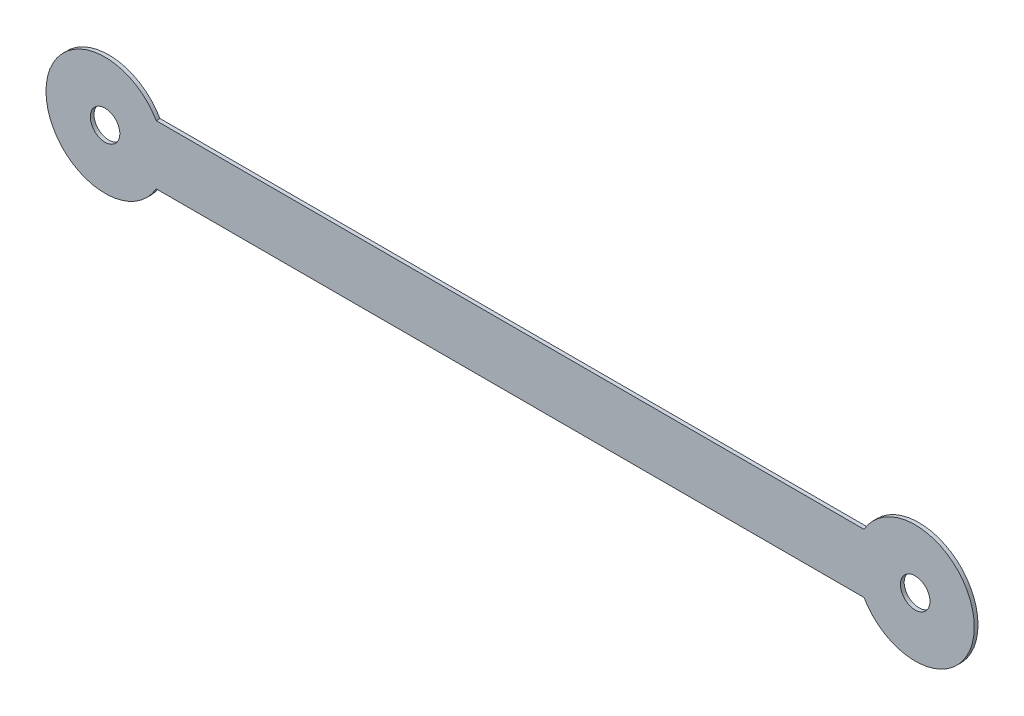
SolidWorks part; units mm, degrees
ref_plane "Front Plane" through (0, 0, 0) normal (0, 0, 1) x (1, 0, 0)
ref_plane "Top Plane" through (0, 0, 0) normal (0, 1, 0) x (1, 0, 0)
ref_plane "Right Plane" through (0, 0, 0) normal (1, 0, 0) x (0, 0, -1)
sketch "Sketch1" plane through (0, 0, 0) normal (0, 0, 1) x (1, 0, 0)
  line L0 (0, 0) -> (54.864, 0) construction
  line L1 (0, 4) -> (54.864, 4)
  line L2 (0, -4) -> (54.864, -4)
  circle A0 centre (0, 0) radius 1
  circle A1 centre (54.864, 0) radius 1
  arc A2 (0, 4) -> (0, -4) centre (0, 0) ccw
  arc A3 (54.864, -4) -> (54.864, 4) centre (54.864, 0) ccw
  point P5 (27.432, 0)
  dimension "D1" = 2
  dimension "D3" = 4
  dimension "D2" = 54.864
extrude "Boss-Extrude1" add sketch "Sketch1" along normal blind 0.254
sketch "Sketch2" plane through (0, 0, 0) normal (0, 0, -1) x (-1, 0, 0)
  line L0 (-54.864, 0) -> (0, 0) construction
  line L1 (-51.3999, 2) -> (-3.4641, 2)
  line L2 (-51.3999, -2) -> (-3.4641, -2)
  line L3 (0, 4) -> (-54.864, 4)
  line L4 (0, -4) -> (-54.864, -4)
  arc A0 (-54.864, -4) -> (-51.3999, -2) centre (-54.864, 0) ccw
  arc A1 (0, 4) -> (-3.4641, 2) centre (0, 0) ccw
  arc A2 (-3.4641, -2) -> (0, -4) centre (0, 0) ccw
  arc A3 (-51.3999, 2) -> (-54.864, 4) centre (-54.864, 0) ccw
  dimension "D1" = 4
extrude "Cut-Extrude1" cut sketch "Sketch2" against normal through all
equation "\"orig_diameter\"= 50.8mm"
equation "\"scale_factor\"= 1.08"
equation "\"d\"= \"orig_diameter\" * \"scale_factor\""
equation "\"D2@Sketch1\"=\"d\""
